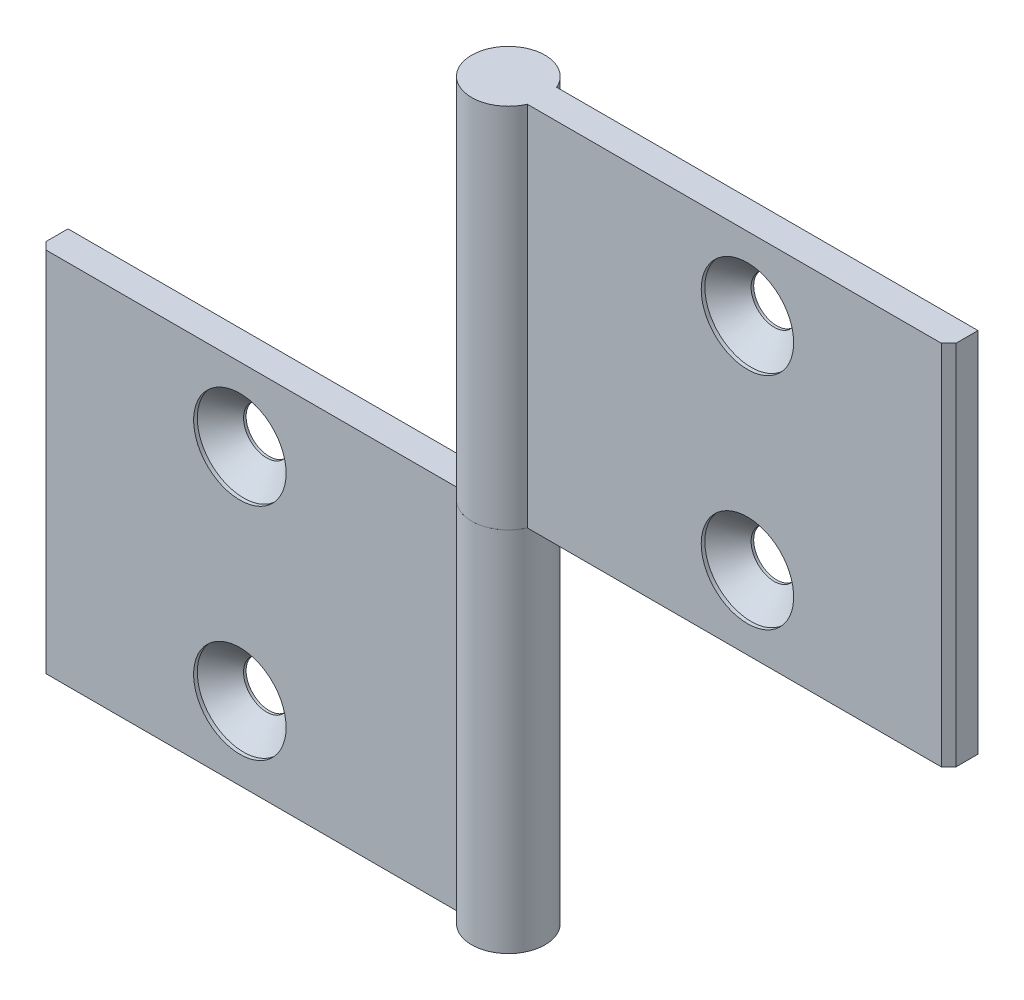
SolidWorks part; units mm, degrees
material "Алюминиевый сплав"
ref_plane "Спереди" through (0, 0, 0) normal (0, 0, 1) x (1, 0, 0)
ref_plane "Сверху" through (0, 0, 0) normal (0, 1, 0) x (1, 0, 0)
ref_plane "Справа" through (0, 0, 0) normal (1, 0, 0) x (0, 0, -1)
sketch "Эскиз1" plane through (0, 0, 0) normal (0, 1, 0) x (1, 0, 0)
  line L0 (-4.5826, 2) -> (-62, 2)
  line L1 (-62, 2) -> (-62, -1)
  line L2 (-62, -1) -> (-61, -2)
  line L3 (-61, -2) -> (-4.5826, -2)
  line L5 (-33.2913, 2) -> (-33.2913, -2) construction
  arc A0 (-4.5826, -2) -> (-4.5826, 2) centre (0, 0) ccw
  point P1 (-33.2913, 0)
  dimension "D5" = 5
  dimension "D1" = 57
  dimension "D2" = 4
  dimension "D3" = 3
  dimension "D4" = 45
extrude "Бобышка-Вытянуть1" add sketch "Эскиз1" along normal mid plane 50
hole_wizard "Зенковка для винта с полупотайной головкой M61" positions "Эскиз4" profile "Эскиз6" countersink size "M6" standard "ISO" end condition through all
sketch "Эскиз4" plane through (0, 0, 2) normal (0, 0, 1) x (1, 0, 0)
  line L0 (-34.5826, 15) -> (-34.5826, -15)
  line L2 (0.2087, -18.4577) -> (0.2087, 25) construction
  line L4 (5, 25) -> (-4.5826, 25) construction
  line L5 (-4.5826, 25) -> (-4.5826, -25) construction
  point P0 (-34.5826, 15)
  point P2 (-34.5826, -15)
  point P9 (-34.5826, 0)
  dimension "D1" = 30
  dimension "D2" = 30
sketch "Эскиз6" plane through (-34.5826, 15, 2) normal (1, 0, 0) x (0, -1, 0)
  line L0 (0, 0) -> (0, 7)
  line L1 (0, 7) -> (3.15, 7)
  line L2 (3.15, 7) -> (3.15, 3.65)
  line L3 (3.15, 3.65) -> (6.3, 0.5)
  line L4 (6.3, 0.5) -> (6.3, 0)
  line L6 (6.3, 0) -> (0, 0)
  line L7 (-3.15, 3.65) -> (-6.3, 0.5) construction
  line L11 (0, -6.35) -> (0, 107.95) construction
  dimension "Диаметр сквозного отверстия" = 6.3
  dimension "Глубина сквозного отверстия" = 7
  dimension "Диаметр зенковки" = 12.6
  dimension "Угол зенковки" = 90
  dimension "Утопленность" = 0.5
sketch "Угол раскрытия" plane through (0, 25, 0) normal (0, 1, 0) x (1, 0, 0)
  line L0 (0, 0) -> (0, -10)
  line L7 (-4.5826, 2) -> (-62, 2) construction
  dimension "D1" = 10
  dimension "D2" = 90
pattern_circular "Круговой массив1" count 2 over 360 about axis through (0, 25, 0) along (0, 0, 1) of bodies 106
